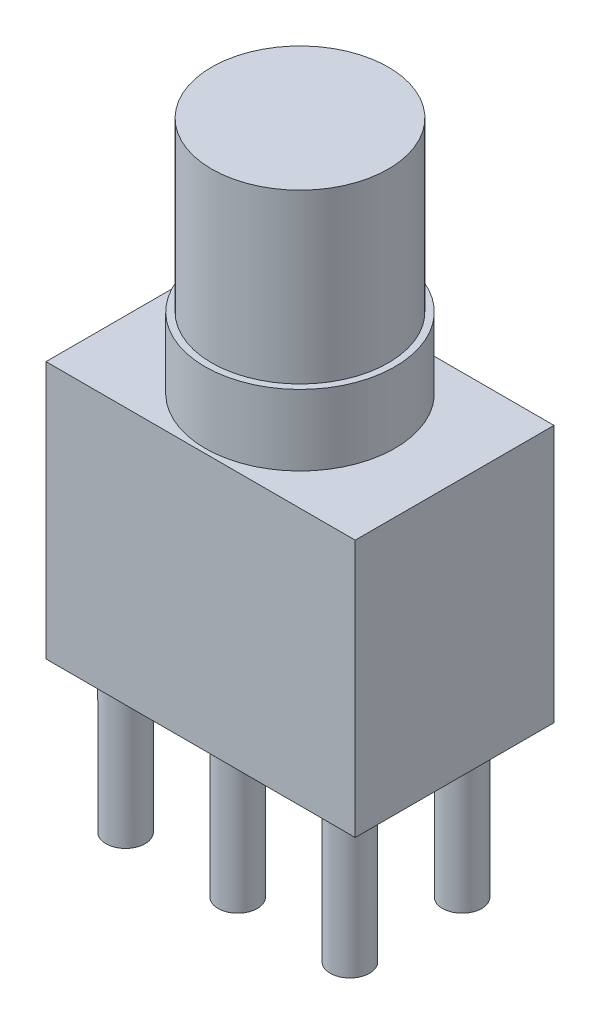
SolidWorks part; units mm, degrees
ref_plane "Front Plane" through (0, 0, 0) normal (0, 0, 1) x (1, 0, 0)
ref_plane "Top Plane" through (0, 0, 0) normal (0, 1, 0) x (1, 0, 0)
ref_plane "Right Plane" through (0, 0, 0) normal (1, 0, 0) x (0, 0, -1)
sketch "Sketch1" plane through (0, 0, 0) normal (0, 1, 0) x (1, 0, 0)
  line L1 (0, 0) -> (7, 0)
  line L2 (0, 0) -> (0, -4.5)
  line L3 (0, -4.5) -> (7, -4.5)
  line L4 (7, 0) -> (7, -4.5)
  dimension "D1" = 7
  dimension "D2" = 4.5
extrude "Boss-Extrude1" add sketch "Sketch1" along normal blind 5.83
sketch "Sketch2" plane through (0, 5.83, 0) normal (0, 1, 0) x (1, 0, 0)
  line L0 (0, 0) -> (0, -4.5) construction
  line L2 (0, -4.5) -> (7, -4.5) construction
  circle A0 centre (3.5, -2.25) radius 2.15
  dimension "D1" = 4.3
  dimension "D2" = 3.5
  dimension "D3" = 2.25
extrude "Boss-Extrude2" add sketch "Sketch2" along normal blind 1.6
sketch "Sketch3" plane through (0, 7.43, 0) normal (0, 1, 0) x (1, 0, 0)
  line L0 (7, 0) -> (0, 0) construction
  line L1 (0, 0) -> (0, -4.5) construction
  circle A0 centre (3.5, -2.25) radius 2
  dimension "D1" = 4
  dimension "D2" = 2.25
  dimension "D3" = 3.5
extrude "Boss-Extrude3" add sketch "Sketch3" along normal blind 3.8
sketch "Sketch4" plane through (0, 0, 0) normal (0, -1, 0) x (1, 0, 0)
  line L1 (0, 0) -> (0, 4.5) construction
  line L2 (0, 4.5) -> (7, 4.5) construction
  line L3 (-2.4407, 2.43) -> (9.2182, 2.43) construction
  circle A0 centre (1, 3.7) radius 0.445
  circle A1 centre (3.54, 3.7) radius 0.445
  circle A2 centre (6.08, 3.7) radius 0.445
  circle A3 centre (6.08, 1.16) radius 0.445
  circle A4 centre (3.54, 1.16) radius 0.445
  circle A5 centre (1, 1.16) radius 0.445
  dimension "D1" = 0.89
  dimension "D2" = 0.89
  dimension "D3" = 0.89
  dimension "D7" = 0.8
  dimension "D4" = 1
  dimension "D5" = 2.54
  dimension "D6" = 2.54
  dimension "D8" = 0.8
  dimension "D9" = 0.8
  dimension "D10" = 2.07
extrude "Boss-Extrude4" add sketch "Sketch4" along normal blind 3.3
